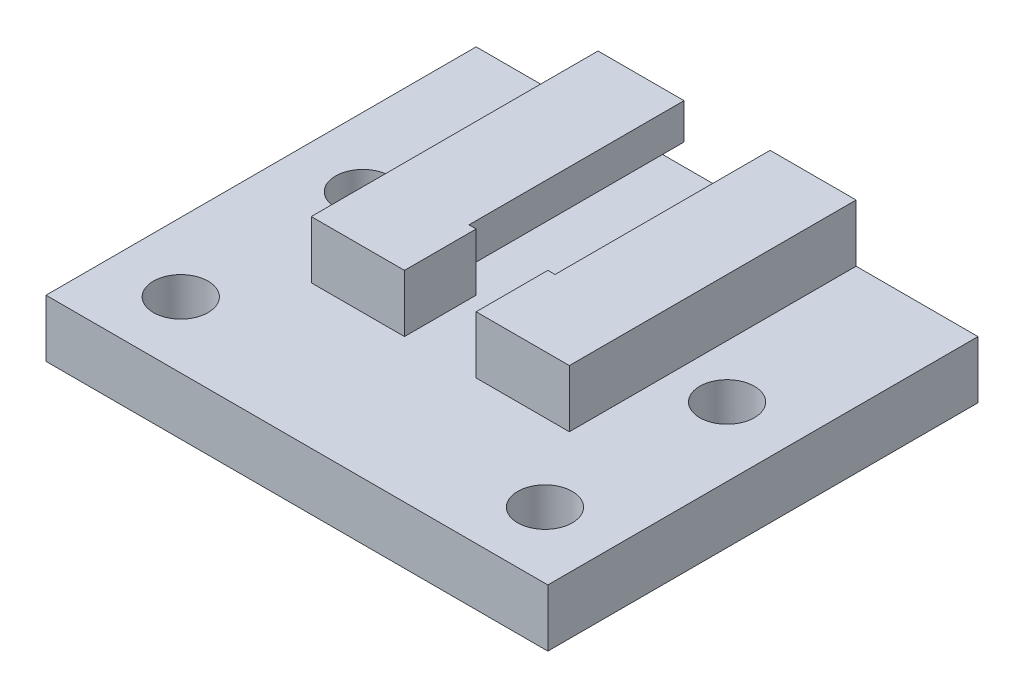
SolidWorks part; units mm, degrees
ref_plane "Front Plane" through (0, 0, 0) normal (0, 0, 1) x (1, 0, 0)
ref_plane "Top Plane" through (0, 0, 0) normal (0, 1, 0) x (1, 0, 0)
ref_plane "Right Plane" through (0, 0, 0) normal (1, 0, 0) x (0, 0, -1)
sketch "Sketch1" plane through (0, 0, 0) normal (0, 1, 0) x (1, 0, 0)
  line L1 (0, 0) -> (18, 0)
  line L2 (0, 0) -> (0, 15)
  line L3 (0, 15) -> (18, 15)
  line L4 (18, 0) -> (18, 15)
  dimension "D1" = 18
  dimension "D2" = 15
extrude "Boss-Extrude1" add sketch "Sketch1" along normal blind 8
sketch "Sketch2" plane through (0, 0, 0) normal (0, 0, 1) x (1, 0, 0)
  line L0 (0, 0) -> (18, 0) construction
  line L1 (4, 5.5) -> (14, 5.5)
  line L2 (4, 5.5) -> (4, 3.5)
  line L3 (4, 3.5) -> (14, 3.5)
  line L4 (14, 5.5) -> (14, 3.5)
  line L5 (0, 8) -> (18, 8) construction
  line L6 (6, 8) -> (12, 8)
  line L7 (6, 8) -> (6, 5.5)
  line L8 (6, 5.5) -> (12, 5.5)
  line L9 (12, 8) -> (12, 5.5)
  line L10 (0, 8) -> (0, 0) construction
  point P12 (9, 0)
  point P13 (9, 3.5)
  point P14 (9, 8)
  line M11 (18, 8) -> (0, 8)
  dimension "D1" = 3.5
  dimension "D2" = 2
  dimension "D3" = 6
  dimension "D4" = 4
extrude "Cut-Extrude1" cut sketch "Sketch2" against normal through all both and the other way through all contours L9 L7 L1 M11 | L4 L1 L2 L3
sketch "Sketch4" plane through (0, 0, 0) normal (0, 0, 1) x (1, 0, 0)
  line L1 (0, 8) -> (18, 8)
  line L2 (0, 8) -> (0, 0)
  line L3 (0, 0) -> (18, 0)
  line L4 (18, 8) -> (18, 0)
  line L5 (6.5, 8) -> (11.5, 8)
  line L6 (6.5, 8) -> (6.5, 0)
  line L7 (6.5, 0) -> (11.5, 0)
  line L8 (11.5, 8) -> (11.5, 0)
  point P10 (9, 8)
  point P11 (9, 8)
  line M1 (12, 8) -> (12, 5.5)
  line M2 (12, 5.5) -> (14, 5.5)
  line M3 (14, 5.5) -> (14, 3.5)
  line M4 (14, 3.5) -> (4, 3.5)
  line M5 (4, 3.5) -> (4, 5.5)
  line M6 (4, 5.5) -> (6, 5.5)
  line M7 (6, 5.5) -> (6, 8)
  line M8 (6, 8) -> (0, 8)
  line M9 (0, 8) -> (0, 0)
  line M10 (0, 0) -> (18, 0)
  line M11 (18, 0) -> (18, 8)
  line M12 (18, 8) -> (12, 8)
  dimension "D1" = 5
extrude "Boss-Extrude2" add sketch "Sketch4" along normal blind 5 contours L8 L6 L3 M4 | L8 M4 M10 M11 M12 M1 M2 M3 | L6 M4 M5 M6 M7 M8 M9 M10 | L6 L1 M7 M6 M5 M4 | L1 L8 M4 M3 M2 M1
sketch "Sketch5" plane through (0, 0, 0) normal (0, -1, 0) x (-1, 0, 0)
  line L0 (-18, 15) -> (0, 15) construction
  line L1 (8.5, 15) -> (-26.5, 15)
  line L2 (8.5, 15) -> (8.5, -15)
  line L3 (8.5, -15) -> (-26.5, -15)
  line L4 (-26.5, 15) -> (-26.5, -15)
  line L5 (0, -5) -> (-18, -5) construction
  point P8 (-9, -5)
  point P9 (-9, -15)
  dimension "D1" = 35
  dimension "D2" = 30
extrude "Boss-Extrude3" add sketch "Sketch5" against normal blind 4
sketch "Sketch6" plane through (0, 0, 0) normal (0, -1, 0) x (-1, 0, 0)
  line L0 (-26.5, -15) -> (8.5, -15) construction
  line L1 (3.7, -10.4) -> (-21.7, -10.4) construction
  line L2 (3.7, -10.4) -> (3.7, 2.3) construction
  line L3 (3.7, 2.3) -> (-21.7, 2.3) construction
  line L4 (-21.7, -10.4) -> (-21.7, 2.3) construction
  line L5 (-26.5, 15) -> (8.5, 15) construction
  circle A0 centre (3.7, 2.3) radius 1.905
  circle A1 centre (-21.7, -10.4) radius 1.905
  circle A2 centre (3.7, -10.4) radius 1.905
  circle A3 centre (-21.7, 2.3) radius 1.905
  point P12 (0, 0)
  point P13 (0, 0)
  point P14 (0, 0)
  point P15 (0, 0)
  point P16 (-9, -15)
  point P17 (-9, -10.4)
  dimension "D2" = 3.81
  dimension "D1" = 25.4
  dimension "D3" = 12.7
  dimension "D4" = 12.7
extrude "Cut-Extrude2" cut sketch "Sketch6" against normal through all both
